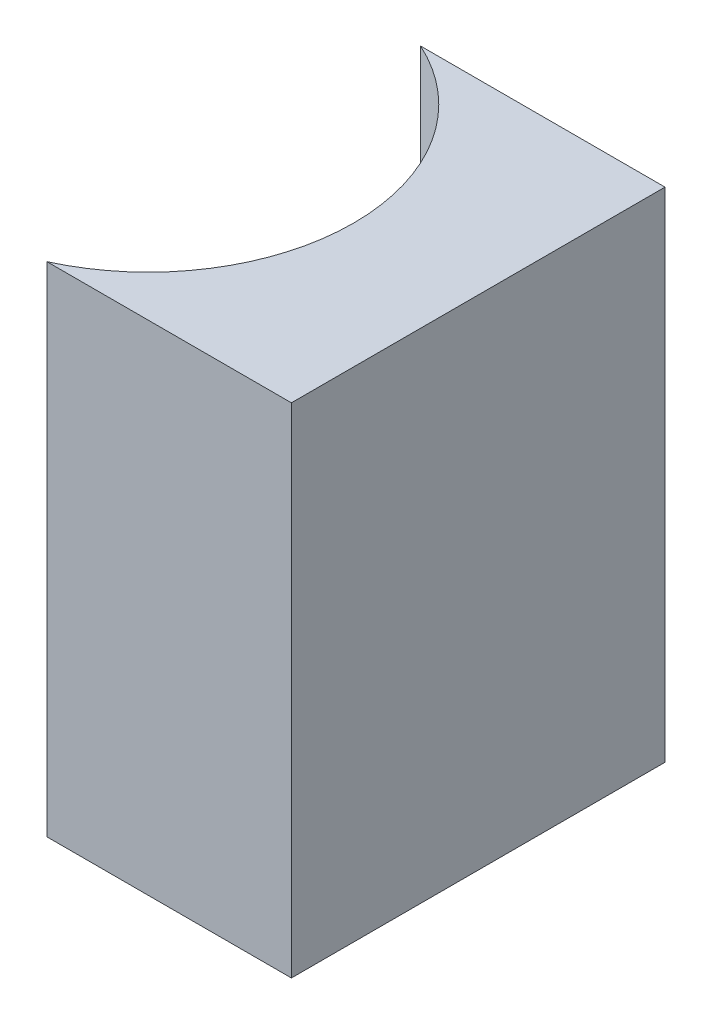
SolidWorks part; units mm, degrees
ref_plane "前视基准面" through (0, 0, 0) normal (0, 0, 1) x (1, 0, 0)
ref_plane "上视基准面" through (0, 0, 0) normal (0, 1, 0) x (1, 0, 0)
ref_plane "右视基准面" through (0, 0, 0) normal (1, 0, 0) x (0, 0, -1)
sketch "草图1" plane through (0, 0, 0) normal (0, 1, 0) x (1, 0, 0)
  line L0 (0, 0) -> (0, -6)
  line L1 (0, 0) -> (-3.9252, 0)
  line L2 (0, -6) -> (-3.9252, -6)
  line L3 (3.924, -3) -> (-6.2059, -3) construction
  arc A0 (-3.9252, -6) -> (-3.9252, 0) centre (-5.3, -3) ccw
  point P7 (-2, -3)
  point P8 (0, -3)
  dimension "D2" = 3.3
  dimension "D3" = 2
  dimension "D1" = 6
extrude "凸台-拉伸1" add sketch "草图1" along normal blind 8
